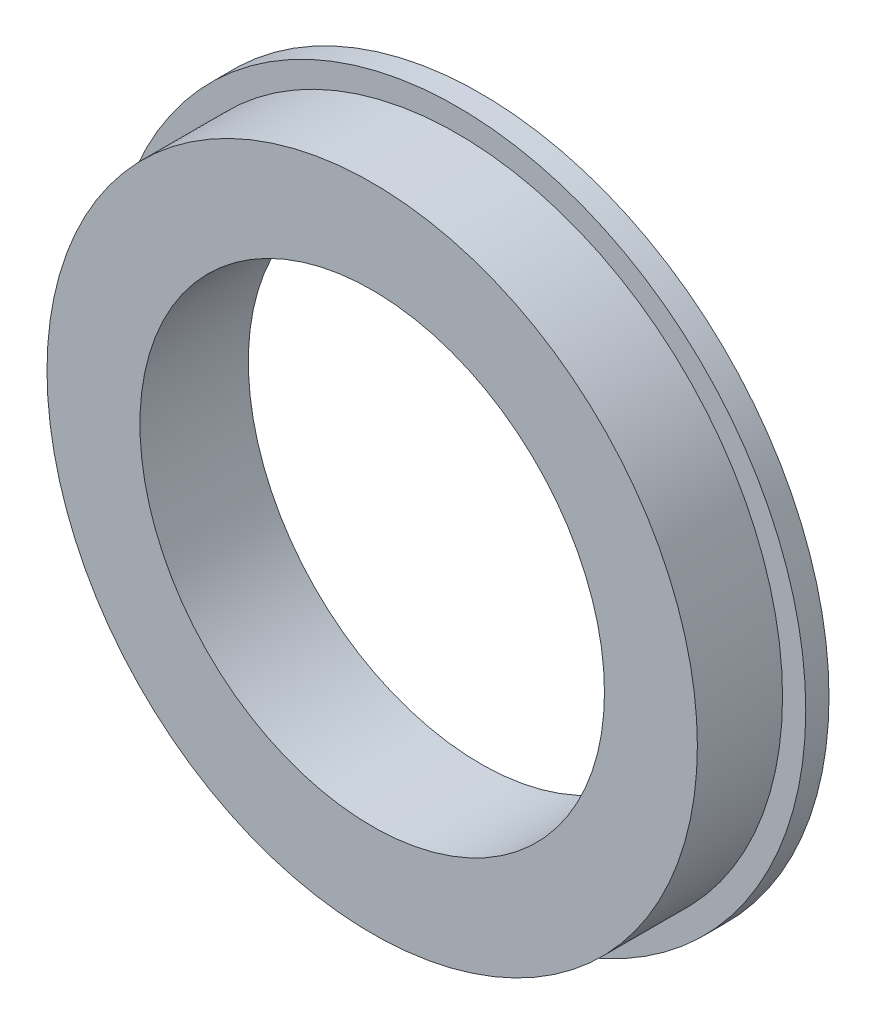
SolidWorks part; units mm, degrees
material "镀铬不锈钢"
ref_plane "前视基准面" through (0, 0, 0) normal (0, 0, 1) x (1, 0, 0)
ref_plane "上视基准面" through (0, 0, 0) normal (0, 1, 0) x (1, 0, 0)
ref_plane "右视基准面" through (0, 0, 0) normal (1, 0, 0) x (0, 0, -1)
sketch "草图1" plane through (0, 0, 0) normal (0, 0, 1) x (1, 0, 0)
  circle A1 centre (0, 0) radius 15
  circle A2 centre (0, 0) radius 21
  dimension "D1" = 30
  dimension "D2" = 42
extrude "凸台-拉伸1" add sketch "草图1" along normal blind 7
sketch "草图2" plane through (0, 0, 0) normal (0, 0, 1) x (1, 0, 0)
  circle A0 centre (0, 0) radius 22.5
  circle A2 centre (0, 0) radius 21 construction
  circle A3 centre (0, 0) radius 21
  dimension "D1" = 45
extrude "凸台-拉伸2" add sketch "草图2" along normal blind 1.5
